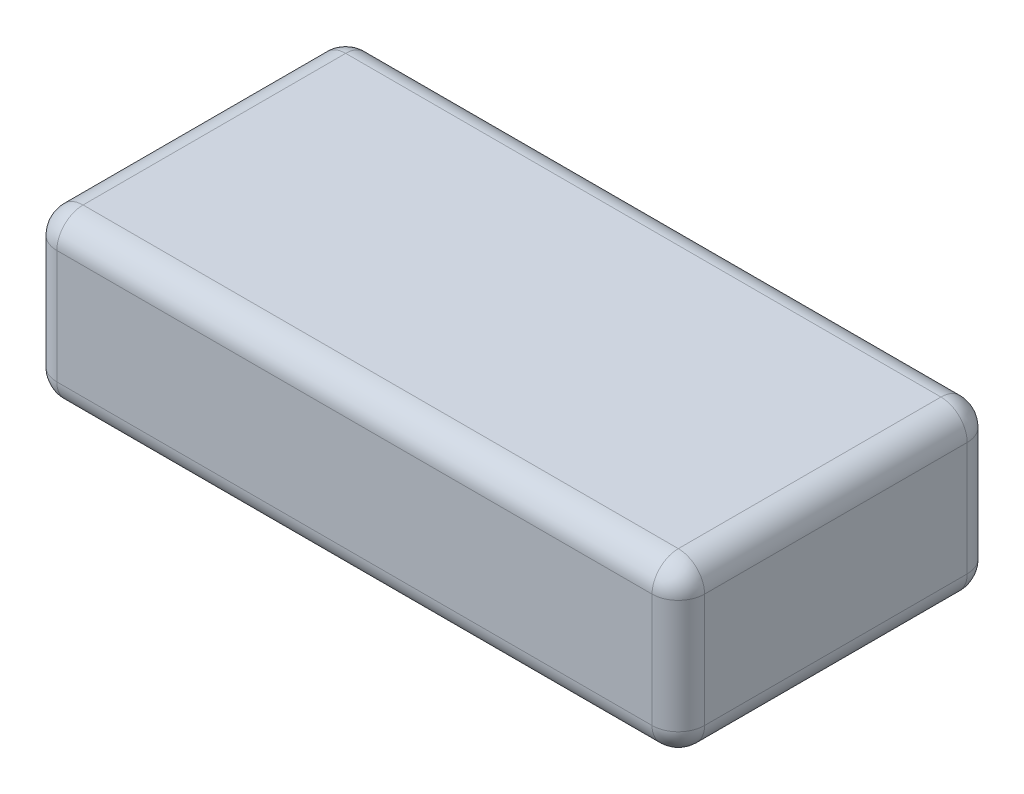
SolidWorks part; units mm, degrees
ref_plane "Front Plane" through (0, 0, 0) normal (0, 0, 1) x (1, 0, 0)
ref_plane "Top Plane" through (0, 0, 0) normal (0, 1, 0) x (1, 0, 0)
ref_plane "Right Plane" through (0, 0, 0) normal (1, 0, 0) x (0, 0, -1)
sketch "Sketch1" plane through (0, 0, 0) normal (0, 1, 0) x (1, 0, 0)
  line L1 (-37, -18) -> (37, -18)
  line L2 (-37, -18) -> (-37, 18)
  line L3 (-37, 18) -> (37, 18)
  line L4 (37, -18) -> (37, 18)
  line L5 (0, 18) -> (0, -18) construction
  line L6 (-37, 0) -> (37, 0) construction
  point P0 (0, 0)
  dimension "D1" = 74
  dimension "D2" = 36
extrude "Boss-Extrude1" add sketch "Sketch1" along normal blind 19
fillet "Fillet1" radius 3 12 edges at (0, 0, -18) (-37, 0, 0) (0, 0, 18) (37, 0, 0) (0, 19, 18) (-37, 19, 0) (0, 19, -18) (37, 19, 0) (37, 9.5, -18) (37, 9.5, 18) (-37, 9.5, -18) (-37, 9.5, 18)
